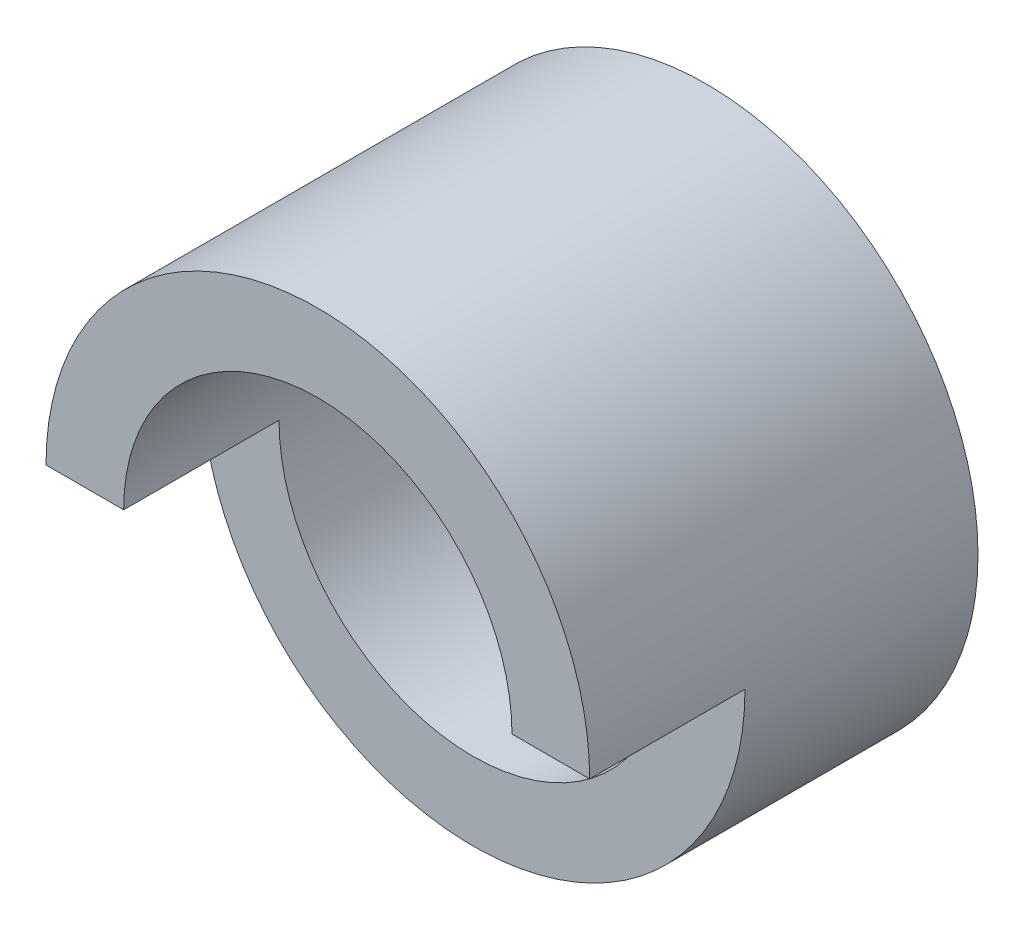
SolidWorks part; units mm, degrees
ref_plane "Front" through (0, 0, 0) normal (0, 0, 1) x (1, 0, 0)
ref_plane "Top" through (0, 0, 0) normal (0, 1, 0) x (1, 0, 0)
ref_plane "Right" through (0, 0, 0) normal (1, 0, 0) x (0, 0, -1)
sketch "Sketch1" plane through (0, 0, 0) normal (0, 0, 1) x (1, 0, 0)
  circle A0 centre (0, 0) radius 7
  circle A1 centre (0, 0) radius 5
  dimension "D1" = 10
  dimension "D2" = 14
extrude "Boss-Extrude1" add sketch "Sketch1" along normal blind 10
sketch "Sketch3" plane through (0, 0, 0) normal (1, 0, 0) x (0, 0, -1)
  line L1 (-10, -7) -> (-6, -7)
  line L2 (-10, -7) -> (-10, 0)
  line L3 (-10, 0) -> (-6, 0)
  line L4 (-6, -7) -> (-6, 0)
  dimension "D1" = 4
  dimension "D2" = 7
extrude "Cut-Extrude1" cut sketch "Sketch3" against normal mid plane 20
